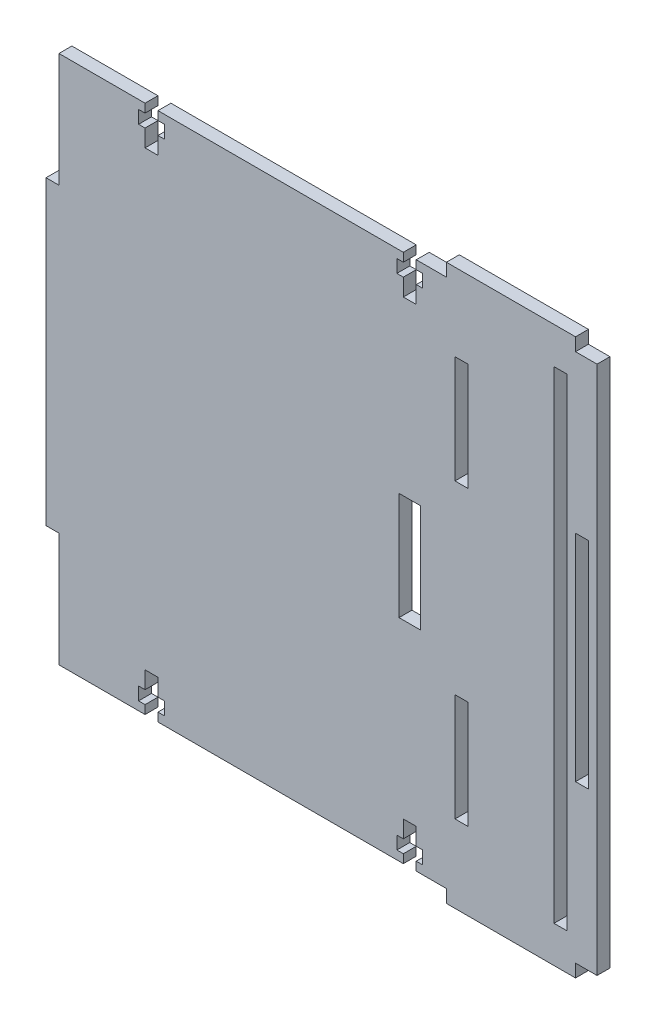
SolidWorks part; units mm, degrees
ref_plane "Front Plane" through (0, 0, 0) normal (0, 0, 1) x (1, 0, 0)
ref_plane "Top Plane" through (0, 0, 0) normal (0, 1, 0) x (1, 0, 0)
ref_plane "Right Plane" through (0, 0, 0) normal (1, 0, 0) x (0, 0, -1)
sketch "Sketch1" plane through (0, 0, 0) normal (0, 0, 1) x (1, 0, 0)
  line L0 (17.5, 52.5) -> (20.5, 52.5)
  line L1 (-62.5, 61.5) -> (-42.5, 61.5)
  line L2 (-62.5, 61.5) -> (-62.5, 35)
  line L3 (-62.5, -61.5) -> (-42.5, -61.5)
  line L4 (62.5, 61.5) -> (62.5, -61.5)
  line L5 (-39.5, -61.5) -> (17.5, -61.5)
  line L7 (27.5, 64.5) -> (57.5, 64.5)
  line L8 (27.5, 64.5) -> (27.5, 61.5)
  line L9 (27.5, -64.5) -> (57.5, -64.5)
  line L10 (57.5, 64.5) -> (57.5, 61.5)
  line L11 (16.5, 12.5) -> (21.5, 12.5)
  line L12 (-39.5, -59.5) -> (-38, -59.5)
  line L13 (-65.5, 35) -> (-62.5, 35)
  line L14 (-65.5, 35) -> (-65.5, -35)
  line L15 (-65.5, -35) -> (-62.5, -35)
  line L17 (20.5, 61.5) -> (27.5, 61.5)
  line L18 (27.5, -61.5) -> (27.5, -64.5)
  line L20 (-42.5, 61.5) -> (-42.5, 59.5)
  line L21 (-42.5, 52.5) -> (-39.5, 52.5)
  line L22 (-39.5, 61.5) -> (-39.5, 59.5)
  line L23 (-62.5, -35) -> (-62.5, -61.5)
  line L24 (16.5, 12.5) -> (16.5, -12.5)
  line L25 (-44, 59.5) -> (-42.5, 59.5)
  line L26 (-44, 59.5) -> (-44, 56.5)
  line L27 (-44, 56.5) -> (-42.5, 56.5)
  line L28 (-38, 59.5) -> (-38, 56.5)
  line L29 (-39.5, -56.5) -> (-39.5, -52.5)
  line L30 (20.5, -61.5) -> (27.5, -61.5)
  line L31 (16, 59.5) -> (16, 56.5)
  line L32 (17.5, 61.5) -> (17.5, 59.5)
  line L33 (20.5, 61.5) -> (20.5, 59.5)
  line L34 (20.5, 56.5) -> (20.5, 52.5)
  line L35 (16, 56.5) -> (17.5, 56.5)
  line L36 (16.5, -12.5) -> (21.5, -12.5)
  line L37 (57.5, 61.5) -> (62.5, 61.5)
  line L38 (16, 59.5) -> (17.5, 59.5)
  line L39 (21.5, 12.5) -> (21.5, -12.5)
  line L40 (22, 59.5) -> (22, 56.5)
  line L41 (57.5, -61.5) -> (57.5, -64.5)
  line L42 (20.5, 59.5) -> (22, 59.5)
  line L43 (17.5, 56.5) -> (17.5, 52.5)
  line L44 (16.5, 12.5) -> (21.5, -12.5) construction
  line L45 (16.5, -12.5) -> (21.5, 12.5) construction
  line L46 (22, -59.5) -> (22, -56.5)
  line L47 (16, -59.5) -> (17.5, -59.5)
  line L48 (16, -56.5) -> (17.5, -56.5)
  line L49 (20.5, -61.5) -> (20.5, -59.5)
  line L50 (17.5, -61.5) -> (17.5, -59.5)
  line L51 (16, -59.5) -> (16, -56.5)
  line L52 (17.5, -52.5) -> (20.5, -52.5)
  line L53 (20.5, -59.5) -> (22, -59.5)
  line L54 (57.5, 25) -> (60.5, 25)
  line L55 (57.5, 25) -> (57.5, -25)
  line L56 (57.5, -25) -> (60.5, -25)
  line L57 (-38, -59.5) -> (-38, -56.5)
  line L58 (-44, -56.5) -> (-42.5, -56.5)
  line L59 (-44, -59.5) -> (-44, -56.5)
  line L60 (-44, -59.5) -> (-42.5, -59.5)
  line L61 (-39.5, -61.5) -> (-39.5, -59.5)
  line L62 (-42.5, -52.5) -> (-39.5, -52.5)
  line L63 (-42.5, -61.5) -> (-42.5, -59.5)
  line L64 (32.5, -21.5) -> (29.5, -21.5)
  line L65 (32.5, 21.5) -> (29.5, 21.5)
  line L66 (32.5, 21.5) -> (32.5, 46.5)
  line L67 (32.5, 46.5) -> (29.5, 46.5)
  line L68 (29.5, 21.5) -> (29.5, 46.5)
  line L69 (60.5, 25) -> (60.5, -25)
  line L70 (57.5, 25) -> (60.5, -25) construction
  line L71 (32.5, -21.5) -> (32.5, -46.5)
  line L72 (29.5, -21.5) -> (29.5, -46.5)
  line L73 (32.5, -46.5) -> (29.5, -46.5)
  line L74 (-39.5, 61.5) -> (17.5, 61.5)
  line L75 (-39.5, -56.5) -> (-38, -56.5)
  line L76 (20.5, -56.5) -> (20.5, -52.5)
  line L77 (-42.5, 56.5) -> (-42.5, 52.5)
  line L78 (57.5, -25) -> (60.5, 25) construction
  line L79 (-39.5, 56.5) -> (-38, 56.5)
  line L81 (20.5, 56.5) -> (22, 56.5)
  line L83 (-39.5, 56.5) -> (-39.5, 52.5)
  line L84 (-39.5, 59.5) -> (-38, 59.5)
  line L85 (57.5, -61.5) -> (62.5, -61.5)
  line L86 (-42.5, -56.5) -> (-42.5, -52.5)
  line L89 (20.5, -56.5) -> (22, -56.5)
  line L92 (17.5, -56.5) -> (17.5, -52.5)
  line L94 (52.5, 56) -> (55.5, 56)
  line L95 (52.5, 56) -> (52.5, -56)
  line L96 (52.5, -56) -> (55.5, -56)
  line L97 (55.5, 56) -> (55.5, -56)
  line L98 (52.5, 56) -> (55.5, -56) construction
  line L99 (52.5, -56) -> (55.5, 56) construction
  point P0 (0, 0)
  point P6 (42.5, 0)
  point P11 (-41, 57)
  point P12 (-62.5, 0)
  point P21 (-41, 58)
  point P33 (19, 57)
  point P38 (19, 58)
  point P44 (19, 0)
  point P46 (19, -58)
  point P47 (19, -57)
  point P56 (-41, -58)
  point P57 (-41, -57)
  point P58 (31, 34)
  point P85 (59, 0)
  point P94 (54, 0)
  dimension "D1" = 125
  dimension "D2" = 123
  dimension "D3" = 70
  dimension "D4" = 30
  dimension "D5" = 25
extrude "Boss-Extrude2" add sketch "Sketch1" along normal blind 3
